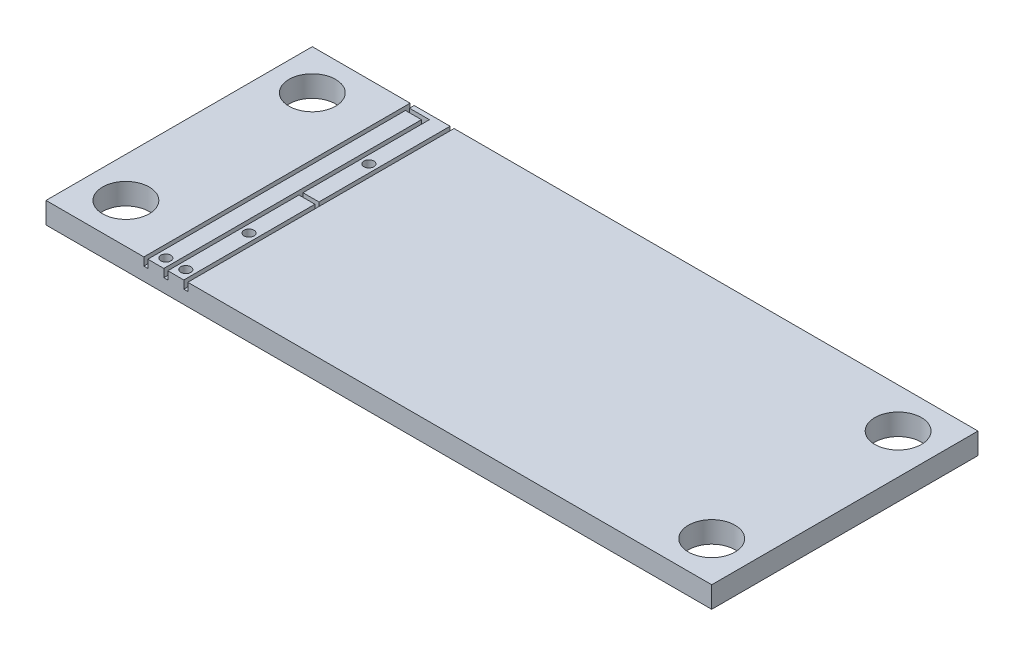
SolidWorks part; units mm, degrees
ref_plane "Front Plane" through (0, 0, 0) normal (0, 0, 1) x (1, 0, 0)
ref_plane "Top Plane" through (0, 0, 0) normal (0, 1, 0) x (1, 0, 0)
ref_plane "Right Plane" through (0, 0, 0) normal (1, 0, 0) x (0, 0, -1)
sketch "Sketch1" plane through (0, 0, 0) normal (0, 1, 0) x (1, 0, 0)
  line L1 (0, 0) -> (50, 0)
  line L2 (0, 0) -> (0, 20)
  line L3 (0, 20) -> (50, 20)
  line L4 (50, 0) -> (50, 20)
  circle A0 centre (3, 17) radius 1.75
  circle A1 centre (47, 3) radius 1.75
  circle A2 centre (3, 3) radius 1.75
  circle A3 centre (47, 17) radius 1.75
  dimension "D3" = 3.5
  dimension "D1" = 20
  dimension "D2" = 50
  dimension "D4" = 3
  dimension "D5" = 3
  dimension "D7" = 3
  dimension "D8" = 3
extrude "Boss-Extrude1" add sketch "Sketch1" along normal blind 1.6
sketch "Sketch2" plane through (0, 1.6, 0) normal (0, 1, 0) x (1, 0, 0)
  line L0 (50, 20) -> (0, 20) construction
  line L1 (7.5, 20) -> (10.5, 20)
  line L2 (7.5, 20) -> (7.5, 0)
  line L3 (7.5, 0) -> (10.5, 0)
  line L4 (10.5, 20) -> (10.5, 0)
  line L5 (0, 0) -> (50, 0) construction
  line L6 (0, 20) -> (0, 0) construction
  line L7 (9, 0) -> (9, 19.5)
  line L8 (9, 19.5) -> (7.5, 19.5)
  line L9 (10.5, 10) -> (9, 10)
  line L10 (9.15, 0) -> (9.15, 19.65)
  line L11 (9.15, 19.65) -> (7.5, 19.65)
  line L12 (8.85, 0) -> (8.85, 19.35)
  line L13 (8.85, 19.35) -> (7.5, 19.35)
  line L14 (7.35, 20) -> (7.35, 0)
  line L15 (7.65, 20) -> (7.65, 0)
  line L16 (10.35, 20) -> (10.35, 0)
  line L17 (10.65, 20) -> (10.65, 0)
  line L18 (10.5, 10.15) -> (9, 10.15)
  line L19 (10.5, 9.85) -> (9, 9.85)
  line L20 (7.35, 20) -> (7.65, 20)
  line L21 (10.35, 20) -> (10.65, 20)
  line L22 (7.5, 19.65) -> (7.5, 19.35)
  line L23 (9, 10.15) -> (9, 9.85)
  line L24 (10.5, 10.15) -> (10.5, 9.85)
  line L25 (7.35, 0) -> (7.65, 0)
  line L26 (8.85, 0) -> (9.15, 0)
  line L27 (10.35, 0) -> (10.65, 0)
  point P33 (0, 0)
  point P34 (0, 0)
  point P35 (0, 0)
  point P37 (0, 0)
  point P38 (0, 0)
  point P39 (0, 0)
  point P40 (0, 0)
  point P41 (0, 0)
  point P42 (0, 0)
  point P43 (0, 0)
  point P44 (0, 0)
  point P45 (0, 0)
  point P46 (0, 0)
  point P47 (0, 0)
  point P48 (0, 0)
  point P49 (0, 0)
  dimension "D1" = 7.5
  dimension "D2" = 3
  dimension "D3" = 0.5
  dimension "D4" = 0.15
  dimension "D5" = 0.15
  dimension "D6" = 0.15
  dimension "D7" = 0.15
  dimension "D8" = 0.15
  dimension "D9" = 0.15
  dimension "D10" = 0.15
  dimension "D11" = 0.15
sketch "Sketch3" plane through (0, 1.6, 0) normal (0, 1, 0) x (1, 0, 0)
  line L0 (7.5, 0) -> (10.5, 0) construction
  line L1 (10.5, 10) -> (9, 10) construction
  line L2 (9, 19.5) -> (7.5, 19.5) construction
  line L3 (9.75, 5.5) -> (9.75, 14.5) construction
  line L4 (8.25, 19.5) -> (8.25, 0.75) construction
  circle A0 centre (8.25, 0.75) radius 0.375
  circle A1 centre (9.75, 0.75) radius 0.375
  circle A2 centre (9.75, 5.5) radius 0.375
  circle A3 centre (9.75, 14.5) radius 0.375
  point P8 (8.25, 19.5)
  point P12 (9.75, 10)
  point P16 (9.75, 10)
  dimension "D1" = 0.75
  dimension "D3" = 9
  dimension "D2" = 0.75
extrude "Cut-Extrude1" cut sketch "Sketch3" against normal through all
extrude "Cut-Extrude2" cut sketch "Sketch2" against normal blind 0.6 contours L14 L25 L15 L20 | L12 L13 L22 L11 L10 L26 | L16 L27 L17 L21 | L19 L23 L18 L24
